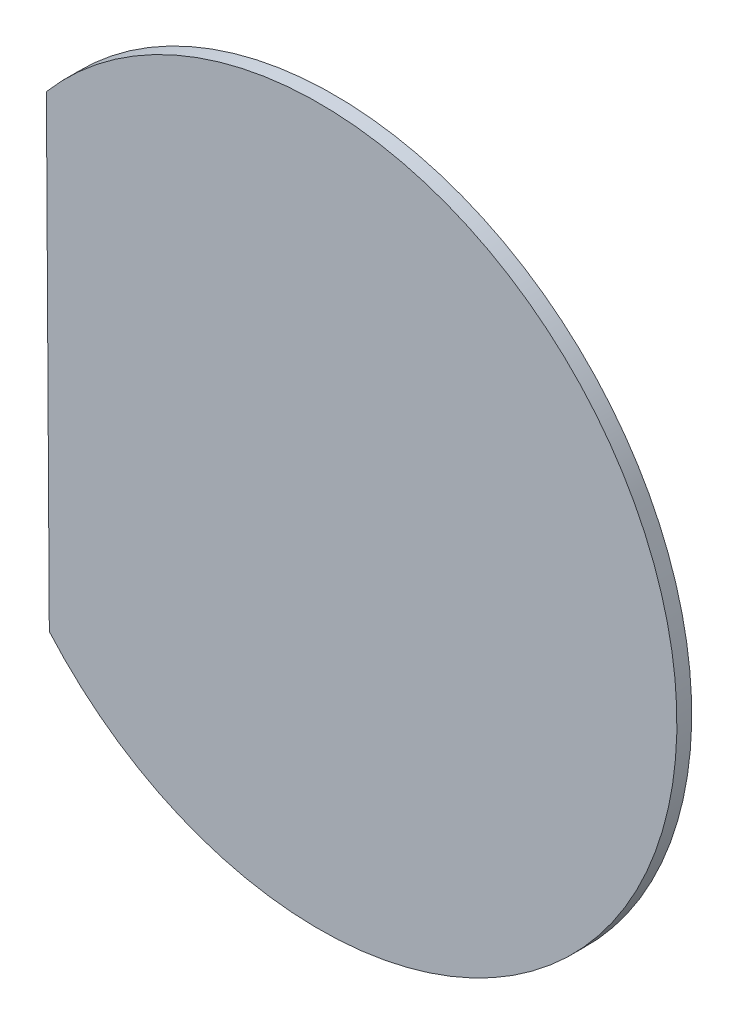
SolidWorks part; units mm, degrees
ref_plane "Plan de face" through (0, 0, 0) normal (0, 0, 1) x (1, 0, 0)
ref_plane "Plan de dessus" through (0, 0, 0) normal (0, 1, 0) x (1, 0, 0)
ref_plane "Plan de droite" through (0, 0, 0) normal (1, 0, 0) x (0, 0, -1)
sketch "Esquisse1" plane through (0, 0, 0) normal (0, 0, 1) x (1, 0, 0)
  line L0 (-110.5893, 93.7817) -> (-109.4064, -95.159)
  circle A0 centre (0, 0) radius 145
  dimension "D1" = 110
  dimension "D2" = 290
extrude "Boss.-Extru.1" add sketch "Esquisse1" along normal blind 6 contours L0 A0
